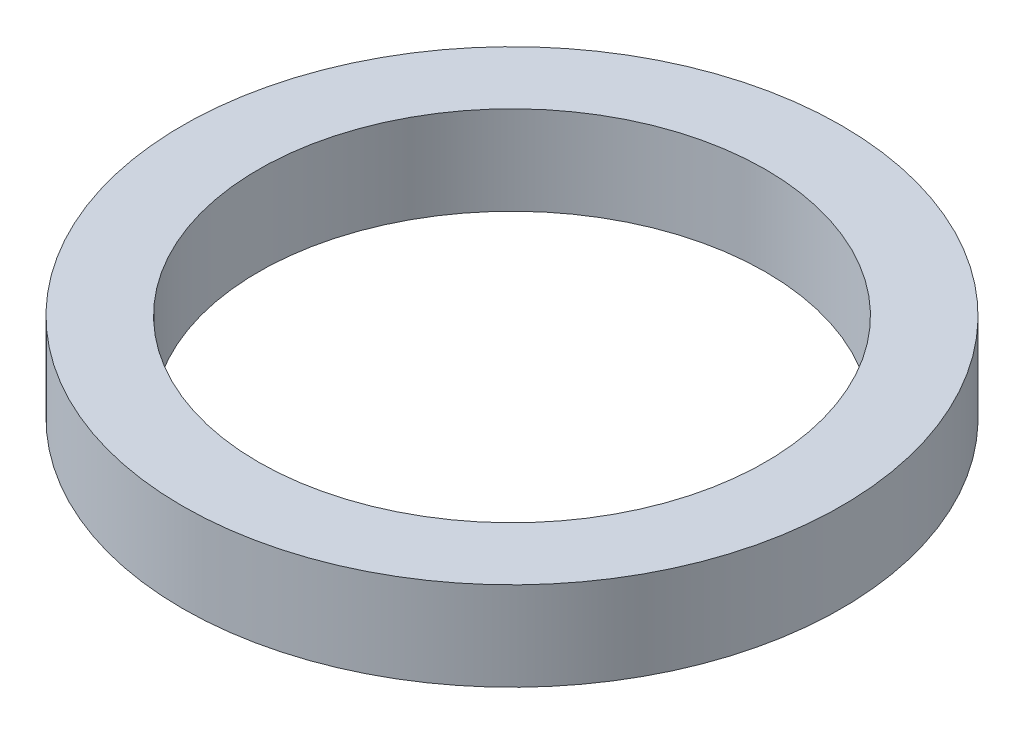
SolidWorks part; units mm, degrees
ref_plane "Front Plane" through (0, 0, 0) normal (0, 0, 1) x (1, 0, 0)
ref_plane "Top Plane" through (0, 0, 0) normal (0, 1, 0) x (1, 0, 0)
ref_plane "Right Plane" through (0, 0, 0) normal (1, 0, 0) x (0, 0, -1)
sketch "Sketch1" plane through (0, 0, 0) normal (0, 1, 0) x (1, 0, 0)
  circle A0 centre (0, 0) radius 26
  circle A1 centre (0, 0) radius 20
  dimension "D1" = 40
  dimension "D2" = 52
extrude "Boss-Extrude1" add sketch "Sketch1" along normal blind 7
